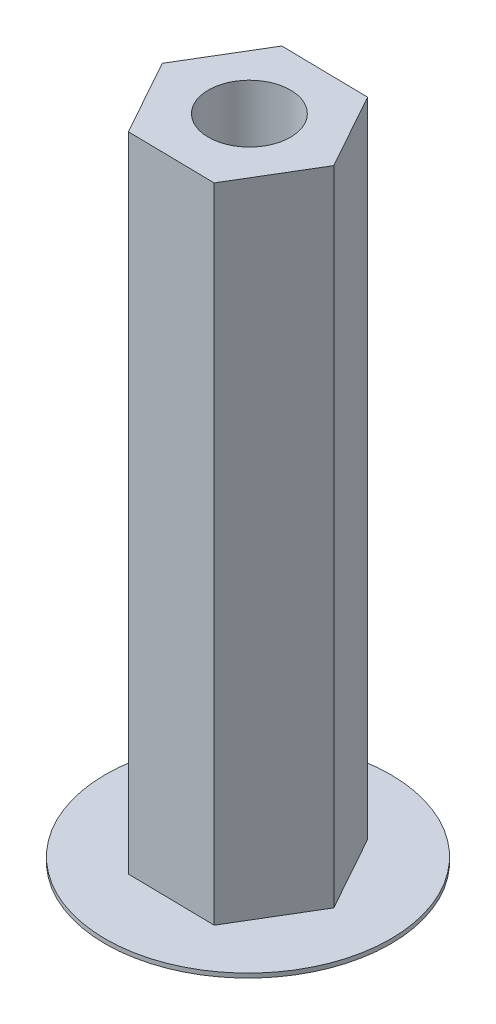
SolidWorks part; units mm, degrees
ref_plane "Front Plane" through (0, 0, 0) normal (0, 0, 1) x (1, 0, 0)
ref_plane "Top Plane" through (0, 0, 0) normal (0, 1, 0) x (1, 0, 0)
ref_plane "Right Plane" through (0, 0, 0) normal (1, 0, 0) x (0, 0, -1)
sketch "Sketch1" plane through (0, 0, 0) normal (0, 1, 0) x (1, 0, 0)
  line L1 (1.9642, -3.5321) -> (4.0409, -0.065)
  line L2 (4.0409, -0.065) -> (2.0768, 3.467)
  line L3 (2.0768, 3.467) -> (-1.9642, 3.5321)
  line L4 (-1.9642, 3.5321) -> (-4.0409, 0.065)
  line L5 (-4.0409, 0.065) -> (-2.0768, -3.467)
  line L6 (-2.0768, -3.467) -> (1.9642, -3.5321)
  circle A0 centre (0, 0) radius 3.5 construction
  circle A1 centre (0, 0.065) radius 1.9
extrude "Boss-Extrude1" add sketch "Sketch1" along normal blind 30
sketch "Sketch3" plane through (0, 0, 0) normal (0, -1, 0) x (-1, 0, 0)
  circle A0 centre (0, 0) radius 6.6074
  circle A1 centre (0, 0) radius 1.965
extrude "Boss-Extrude2" add sketch "Sketch3" against normal blind 0.2
